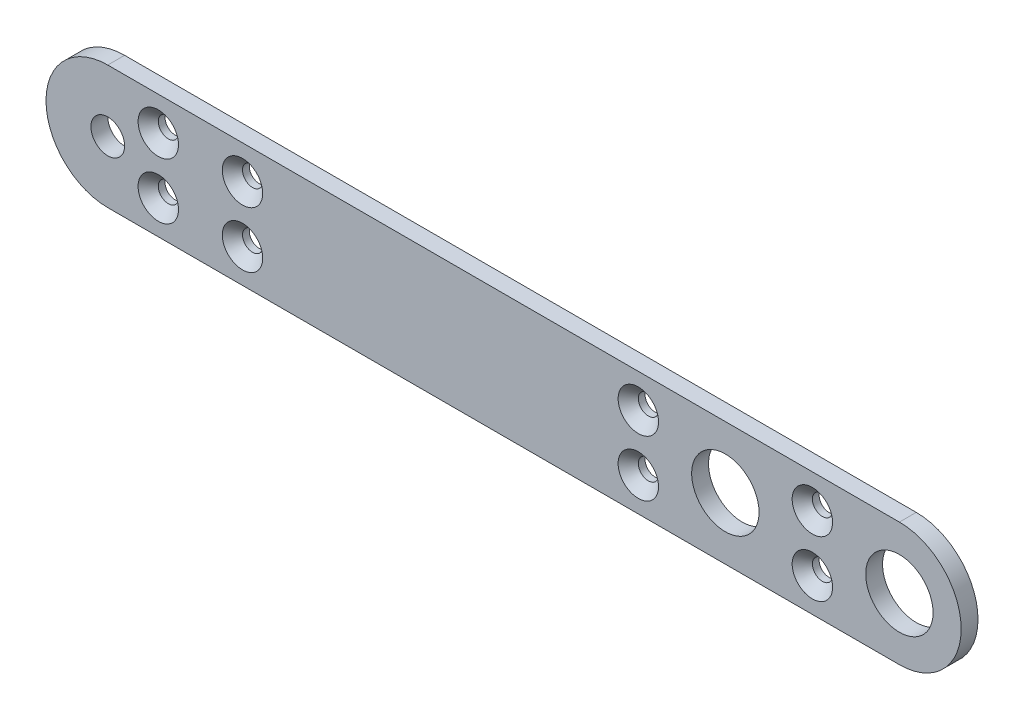
SolidWorks part; units mm, degrees
material "Hexcel AS4C (3000 Filaments)"
ref_plane "Front Plane" through (0, 0, 0) normal (0, 0, 1) x (1, 0, 0)
ref_plane "Top Plane" through (0, 0, 0) normal (0, 1, 0) x (1, 0, 0)
ref_plane "Right Plane" through (0, 0, 0) normal (1, 0, 0) x (0, 0, -1)
sketch "Sketch1" plane through (0, 0, 0) normal (0, 0, 1) x (1, 0, 0)
  line L0 (15.5, 5.5) -> (-55, 5.5)
  line L1 (-55, -5.5) -> (15.5, -5.5)
  line L2 (0, 0) -> (31.9738, 0) construction
  arc A0 (-55, 5.5) -> (-55, -5.5) centre (-55, 0) ccw
  arc A1 (15.5, -5.5) -> (15.5, 5.5) centre (15.5, 0) ccw
  circle A2 centre (-55, 0) radius 1.5
  circle A3 centre (0, 0) radius 3
  circle A4 centre (15.5, 0) radius 3
  dimension "D1" = 6
  dimension "D2" = 15.5
  dimension "D3" = 3
  dimension "D4" = 55
  dimension "D5" = 5.5
extrude "Boss-Extrude1" add sketch "Sketch1" along normal blind 1.5
hole_wizard "CSK for M1.6 Countersunk Flat Head Screw1" positions "Sketch3" profile "Sketch2" countersink size "M1.6" standard "DIN" end condition through all
sketch "Sketch3" plane through (0, 0, 1.5) normal (0, 0, 1) x (1, 0, 0)
  line L0 (0, 0) -> (-68.8863, 0) construction
  line L2 (7.75, -12.0598) -> (7.75, 13.3437) construction
  line L4 (0, 0) -> (0, 9.9697) construction
  circle A0 centre (-55, 0) radius 1.5 construction
  circle A1 centre (0, 0) radius 3 construction
  circle A2 centre (15.5, 0) radius 3 construction
  point P1 (7.75, 2.5)
  point P5 (-7.75, 2.5)
  point P7 (-50.5, 2.5)
  point P11 (-43, 2.5)
  dimension "D1" = 4.5
  dimension "D2" = 12
  dimension "D3" = 5
sketch "Sketch2" plane through (7.75, 2.5, 1.5) normal (1, 0, 0) x (0, -1, 0)
  line L0 (0, 0) -> (0, 1.5)
  line L1 (0, 1.5) -> (0.9, 1.5)
  line L2 (0.9, 1.5) -> (0.9, 0.9)
  line L3 (0.9, 0.9) -> (1.8, 0)
  line L5 (1.8, 0) -> (0, 0)
  line L6 (-0.9, 0.9) -> (-1.8, 0) construction
  line L11 (0, -6.35) -> (0, 107.95) construction
  dimension "Thru Hole Dia." = 1.8
  dimension "Thru Hole Depth" = 1.5
  dimension "Near C'Sink Dia." = 3.6
  dimension "Near C'Sink Angle" = 90
mirror "Mirror1" about plane through (0, 0, 0) normal (0, 1, 0) of "CSK for M1.6 Countersunk Flat Head Screw1"
